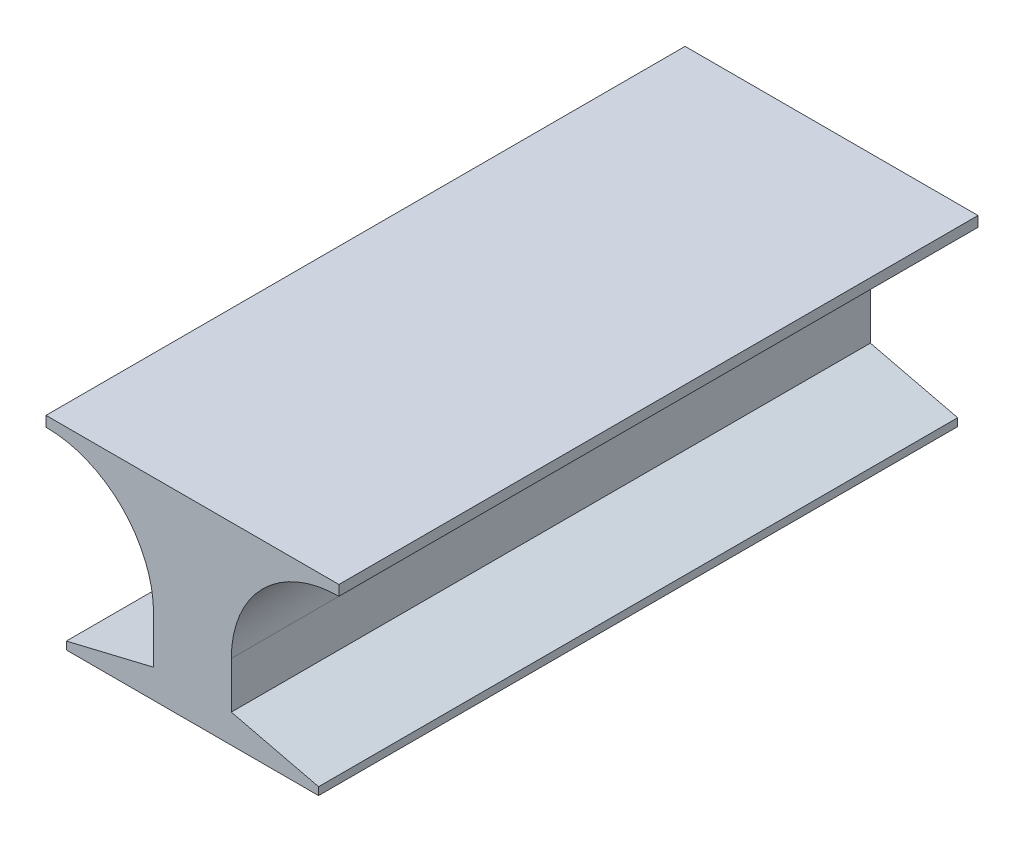
SolidWorks part; units mm, degrees
ref_plane "Front Plane" through (0, 0, 0) normal (0, 0, 1) x (1, 0, 0)
ref_plane "Top Plane" through (0, 0, 0) normal (0, 1, 0) x (1, 0, 0)
ref_plane "Right Plane" through (0, 0, 0) normal (1, 0, 0) x (0, 0, -1)
sketch "Sketch2" plane through (0, 0, 0) normal (0, 1, 0) x (1, 0, 0)
  line L1 (558.8, -1219.2) -> (-558.8, -1219.2)
  line L2 (558.8, -1219.2) -> (558.8, 1219.2)
  line L3 (558.8, 1219.2) -> (-558.8, 1219.2)
  line L4 (-558.8, -1219.2) -> (-558.8, 1219.2)
  line L5 (558.8, -1219.2) -> (-558.8, 1219.2) construction
  line L6 (558.8, 1219.2) -> (-558.8, -1219.2) construction
  point P0 (0, 0)
  dimension "D1" = 2438.4
  dimension "D2" = 1117.6
extrude "Boss-Extrude1" add sketch "Sketch2" along normal blind 736.6
sketch "Sketch3" plane through (0, 0, 1219.2) normal (0, 0, 1) x (1, 0, 0)
  line L0 (-558.8, 0) -> (-558.8, 286.8874) construction
  line L1 (-558.8, 736.6) -> (-558.8, 0) construction
  line L2 (558.8, 0) -> (558.8, 286.8874) construction
  line L3 (-148.2872, 109.5244) -> (-148.2872, 286.8874)
  line L4 (-148.2872, 109.5244) -> (-481.2064, 29.5656)
  line L5 (-481.2064, 29.5656) -> (-481.2064, 0)
  line L6 (-558.8, 0) -> (558.8, 0) construction
  line L7 (-558.8, 697.4003) -> (-558.8, 0)
  line L8 (-558.8, 0) -> (-481.2064, 0)
  line L9 (0, 736.6) -> (0, 0) construction
  line L10 (-558.8, 736.6) -> (558.8, 736.6) construction
  line L11 (558.8, 0) -> (481.2064, 0)
  line L12 (558.8, 697.4003) -> (558.8, 0)
  line L13 (481.2064, 29.5656) -> (481.2064, 0)
  line L14 (148.2872, 109.5244) -> (481.2064, 29.5656)
  line L15 (148.2872, 109.5244) -> (148.2872, 286.8874)
  arc A0 (148.2872, 286.8874) -> (558.8, 697.4003) centre (558.8, 286.8874) cw
  arc A1 (-148.2872, 286.8874) -> (-558.8, 697.4003) centre (-558.8, 286.8874) ccw
  point P5 (-558.8, 0)
extrude "Cut-Extrude1" cut sketch "Sketch3" against normal through all
